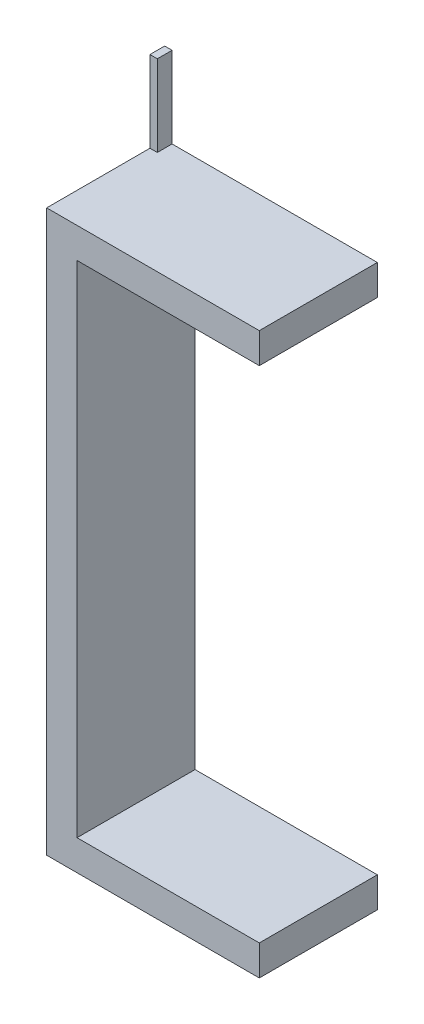
SolidWorks part; units mm, degrees
ref_plane "Front Plane" through (0, 0, 0) normal (0, 0, 1) x (1, 0, 0)
ref_plane "Top Plane" through (0, 0, 0) normal (0, 1, 0) x (1, 0, 0)
ref_plane "Right Plane" through (0, 0, 0) normal (1, 0, 0) x (0, 0, -1)
ref_plane "Plane1" through (0, 0, -60) normal (0, 0, -1) x (-1, 0, 0)
sketch "Sketch1" plane through (0, 0, -60) normal (0, 0, -1) x (-1, 0, 0)
  line L0 (-144.1176, -154.4118) -> (-144.1176, -175)
  line L1 (-144.1176, -175) -> (0, -175)
  line L2 (0, -175) -> (0, 205)
  line L3 (0, 205) -> (-144.1176, 205)
  line L4 (-144.1176, 205) -> (-144.1176, 184.4118)
  line L5 (-144.1176, 184.4118) -> (-20.5882, 184.4118)
  line L6 (-20.5882, 184.4118) -> (-20.5882, -154.4118)
  line L7 (-20.5882, -154.4118) -> (-144.1176, -154.4118)
  dimension "D1" = 380
extrude "Boss-Extrude1" add sketch "Sketch1" against normal blind 80
sketch "Sketch2" plane through (0, 205, 0) normal (0, 1, 0) x (-1, 0, 0)
  line L0 (0, -60) -> (-5, -60)
  line L1 (0, -60) -> (0, -50)
  line L2 (0, -50) -> (-5, -50)
  line L3 (-5, -60) -> (-5, -50)
extrude "Boss-Extrude2" add sketch "Sketch2" along normal blind 55
sketch "Sketch3" plane through (0, 0, 0) normal (-1, 0, 0) x (0, 0, 1)
  circle A0 centre (-54.8482, 179.0018) radius 2
  circle A1 centre (-54.8482, 219.0018) radius 2
